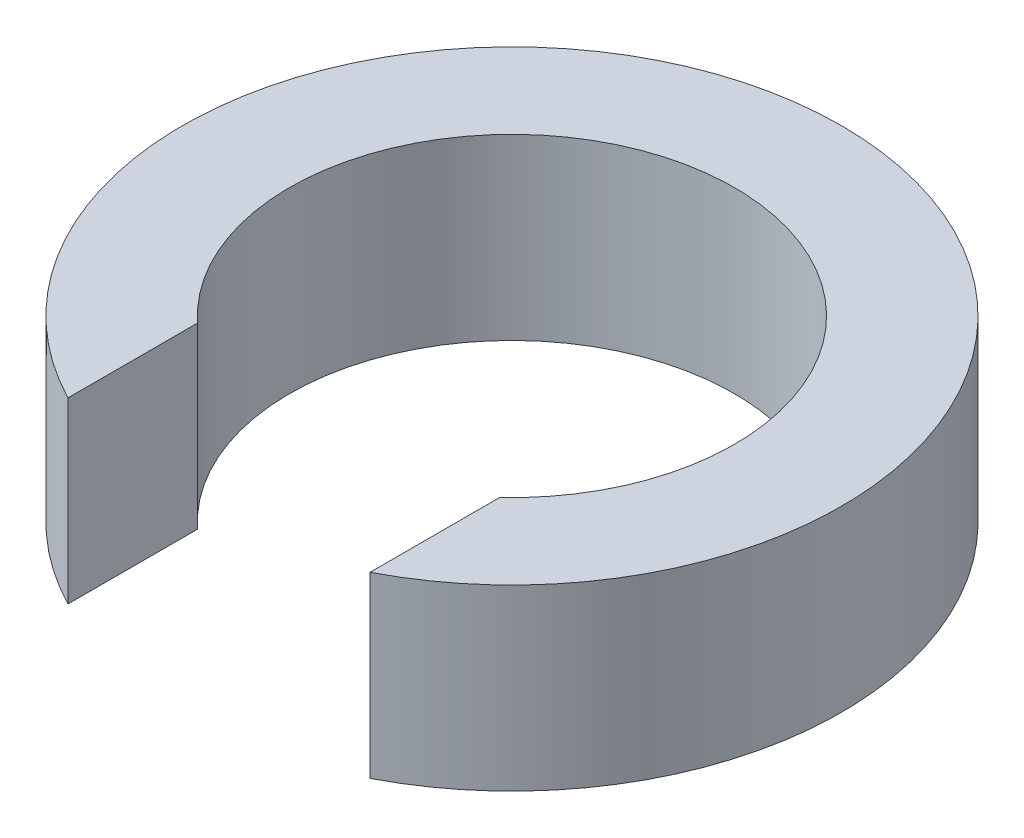
SolidWorks part; units mm, degrees
ref_plane "Front Plane" through (0, 0, 0) normal (0, 0, 1) x (1, 0, 0)
ref_plane "Top Plane" through (0, 0, 0) normal (0, 1, 0) x (1, 0, 0)
ref_plane "Right Plane" through (0, 0, 0) normal (1, 0, 0) x (0, 0, -1)
sketch "Sketch1" plane through (0, 0, 0) normal (0, 1, 0) x (1, 0, 0)
  line L0 (-2.75, -2.9732) -> (-2.75, -5.3327)
  line L1 (2.75, -2.9732) -> (2.75, -5.3327)
  arc A0 (2.75, -2.9732) -> (-2.75, -2.9732) centre (0, 0) ccw
  arc A1 (2.75, -5.3327) -> (-2.75, -5.3327) centre (0, 0) ccw
  dimension "D1" = 8.1
  dimension "D2" = 12
  dimension "D3" = 2.75
  dimension "D4" = 2.75
extrude "Boss-Extrude1" add sketch "Sketch1" along normal blind 3.25
